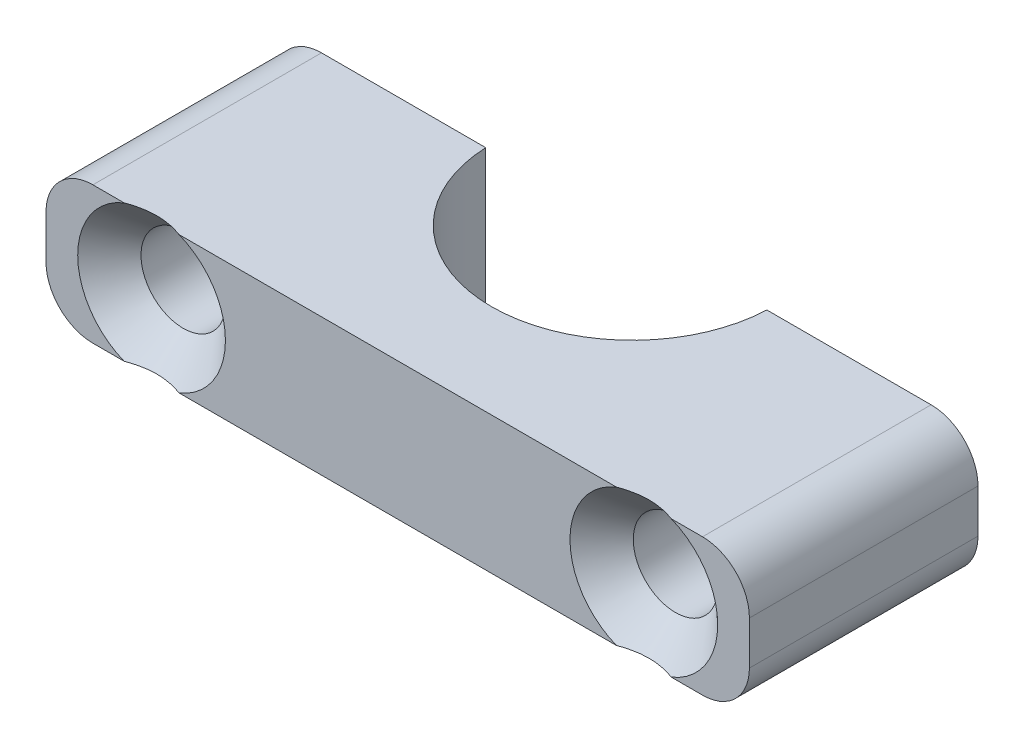
SolidWorks part; units mm, degrees
material "ABS"
ref_plane "Front Plane" through (0, 0, 0) normal (0, 0, 1) x (1, 0, 0)
ref_plane "Top Plane" through (0, 0, 0) normal (0, 1, 0) x (1, 0, 0)
ref_plane "Right Plane" through (0, 0, 0) normal (1, 0, 0) x (0, 0, -1)
sketch "Sketch2" plane through (0, 0, 0) normal (0, 1, 0) x (1, 0, 0)
  line L1 (15, -4.875) -> (-15, -4.875)
  line L2 (15, -4.875) -> (15, 4.875)
  line L3 (15, 4.875) -> (-15, 4.875)
  line L4 (-15, -4.875) -> (-15, 4.875)
  line L5 (0, 4.875) -> (0, -4.875) construction
  line L6 (15, 0) -> (-15, 0) construction
  circle A0 centre (0, 5.125) radius 6
  circle A1 centre (0, 5.125) radius 6.35 construction
  point P0 (0, 0)
  dimension "D2" = 12
  dimension "D1" = 30
  dimension "D3" = 0.25
  dimension "D4" = 4
  dimension "D5" = 0.35
extrude "Boss-Extrude1" add sketch "Sketch2" along normal mid plane 5.85 contours A0 L3 L4 L1 L2
sketch "Sketch4" plane through (0, 0, 4.875) normal (0, 0, -1) x (-1, 0, 0)
  line L0 (15, 2.925) -> (5.9948, -2.925) construction
  line L1 (15, -2.925) -> (5.9948, 2.925) construction
  line L2 (-5.9948, -2.925) -> (-15, 2.925) construction
  line L3 (-5.9948, 2.925) -> (-15, -2.925) construction
  line L4 (5.9948, 2.925) -> (5.9948, -2.925) construction
  line L5 (5.9948, 2.925) -> (-5.9948, 2.925) construction
  point P16 (10.4974, 0)
  point P17 (-10.4974, 0)
hole_wizard "CSK for M3 Flat Head Machine Screw1" positions "Sketch5" profile "Sketch7" countersink size "M3" standard "ANSI Metric" end condition through all
sketch "Sketch5" plane through (0, 0, 4.875) normal (0, 0, 1) x (1, 0, 0)
  point P0 (-10.4974, 0)
  point P3 (10.4974, 0)
sketch "Sketch7" plane through (-10.4974, 0, 4.875) normal (1, 0, 0) x (0, -1, 0)
  line L0 (0, 0) -> (0, 9.75)
  line L1 (0, 9.75) -> (1.8, 9.75)
  line L2 (1.8, 9.75) -> (1.8, 1.35)
  line L3 (1.8, 1.35) -> (3.15, 0)
  line L5 (3.15, 0) -> (0, 0)
  line L6 (-1.8, 1.35) -> (-3.15, 0) construction
  line L11 (0, -6.35) -> (0, 107.95) construction
  dimension "Thru Hole Dia." = 3.6
  dimension "Thru Hole Depth" = 9.75
  dimension "Near C'Sink Dia." = 6.3
  dimension "Near C'Sink Angle" = 90
fillet "Fillet1" radius 2 4 edges at (15, 2.925, 0) (15, -2.925, 0) (-15, -2.925, 0) (-15, 2.925, 0)
